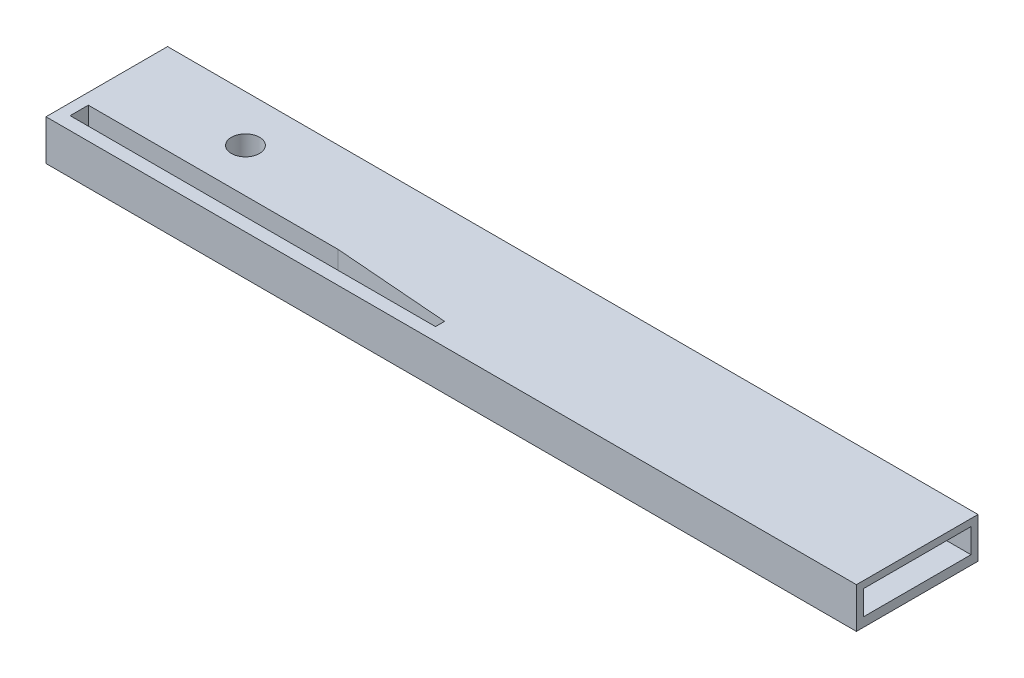
SolidWorks part; units mm, degrees
ref_plane "Front Plane" through (0, 0, 0) normal (0, 0, 1) x (1, 0, 0)
ref_plane "Top Plane" through (0, 0, 0) normal (0, 1, 0) x (1, 0, 0)
ref_plane "Right Plane" through (0, 0, 0) normal (1, 0, 0) x (0, 0, -1)
sketch "Sketch2" plane through (0, 0, 0) normal (0, 1, 0) x (1, 0, 0)
  line L1 (-63.5, 9.525) -> (63.5, 9.525)
  line L2 (-63.5, 9.525) -> (-63.5, -9.525)
  line L3 (-63.5, -9.525) -> (63.5, -9.525)
  line L4 (63.5, 9.525) -> (63.5, -9.525)
  line L5 (-63.5, 9.525) -> (63.5, -9.525) construction
  line L6 (-63.5, -9.525) -> (63.5, 9.525) construction
  point P0 (0, 0)
  dimension "D1" = 127
  dimension "D2" = 19.05
extrude "Boss-Extrude1" add sketch "Sketch2" along normal blind 6.35
sketch "Sketch3" plane through (63.5, 0, 0) normal (1, 0, 0) x (0, 0, -1)
  line L1 (-8.4287, 5.2523) -> (8.4287, 5.2523)
  line L2 (-8.4287, 5.2523) -> (-8.4287, 1.4356)
  line L3 (-8.4287, 1.4356) -> (8.4287, 1.4356)
  line L4 (8.4287, 5.2523) -> (8.4287, 1.4356)
  line L5 (-8.4287, 5.2523) -> (8.4287, 1.4356) construction
  line L6 (-8.4287, 1.4356) -> (8.4287, 5.2523) construction
  point P0 (0, 3.344)
extrude "Cut-Extrude1" cut sketch "Sketch3" against normal blind 6.35
sketch "Sketch4" plane through (0, 6.35, 0) normal (0, 1, 0) x (1, 0, 0)
  line L0 (-22.6377, -4.6364) -> (-4.5059, -6.0621)
  line L1 (-61.7572, -4.6364) -> (-22.6377, -4.6364)
  line L2 (-61.7572, -4.6364) -> (-61.7572, -7.4877)
  line L3 (-61.7572, -7.4877) -> (-4.5059, -7.4877)
  line L4 (-4.5059, -6.0621) -> (-4.5059, -7.4877)
extrude "Cut-Extrude2" cut sketch "Sketch4" against normal through all
sketch "Sketch5" plane through (0, 6.35, 0) normal (0, 1, 0) x (1, 0, 0)
  circle A0 centre (-43.9862, 2.2149) radius 2.2081
extrude "Cut-Extrude3" cut sketch "Sketch5" against normal blind 6.35
